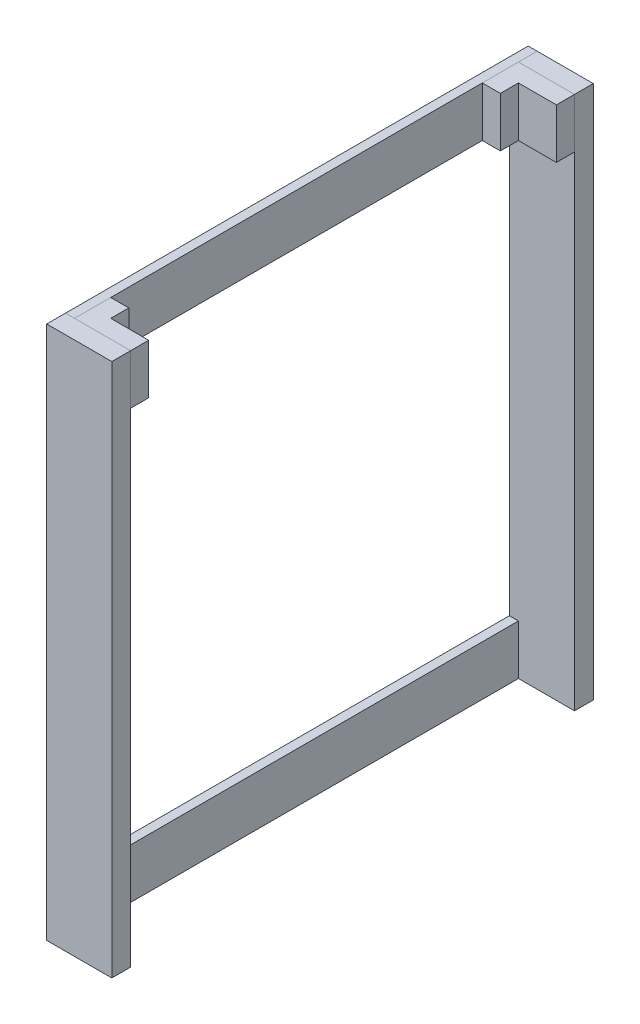
SolidWorks part; units mm, degrees
material "Pine"
ref_plane "Front Plane" through (0, 0, 0) normal (0, 0, 1) x (1, 0, 0)
ref_plane "Top Plane" through (0, 0, 0) normal (0, 1, 0) x (1, 0, 0)
ref_plane "Right Plane" through (0, 0, 0) normal (1, 0, 0) x (0, 0, -1)
sketch "Sketch1" plane through (0, 0, 0) normal (0, 1, 0) x (1, 0, 0)
  line L0 (0, -385) -> (0, 385) construction
  line L1 (-700, 350) -> (700, 350)
  line L2 (-700, 350) -> (-700, -350)
  line L3 (-700, -350) -> (700, -350)
  line L4 (700, 350) -> (700, -350)
  line L6 (-770, 0) -> (770, 0) construction
  dimension "D1" = 700
  dimension "D2" = 1400
  dimension "D3" = 700
  dimension "D4" = 350
ref_plane "Plane1" through (0, -900, 0) normal (0, 1, 0) x (-1, 0, 0)
sketch "Sketch3" plane through (0, -900, 0) normal (0, 1, 0) x (-1, 0, 0)
  line L0 (700, -350) -> (700, 350) construction
  line L1 (700, -350) -> (-700, -350) construction
  line L2 (700, 350) -> (-700, 350) construction
  line L3 (700, 333) -> (610, 333)
  line L4 (700, 333) -> (700, 307)
  line L5 (700, -333) -> (610, -333)
  line L6 (700, -333) -> (700, -307)
  line L7 (700, -307) -> (610, -307)
  line L8 (610, -333) -> (610, -307)
  line L9 (700, 307) -> (610, 307)
  line L10 (610, 333) -> (610, 307)
  dimension "D1" = 26
  dimension "D2" = 90
  dimension "D3" = 17
  dimension "D4" = 17
extrude "Boss-Extrude1" add sketch "Sketch3" along normal offset from surface (738.5 mm away) 31.5 from offset 130 up to plane "Top Plane"
sketch "Sketch5" plane through (0, 0, 0) normal (0, 0, 1) x (1, 0, 0)
  line L1 (-700, -31.5) -> (-687.5, -31.5)
  line L2 (-700, -31.5) -> (-700, -100.5)
  line L3 (-700, -100.5) -> (-687.5, -100.5)
  line L4 (-687.5, -31.5) -> (-687.5, -100.5)
  line L5 (-700, -770) -> (-687.5, -770)
  line L6 (-700, -770) -> (-700, -701)
  line L7 (-700, -701) -> (-687.5, -701)
  line L8 (-687.5, -770) -> (-687.5, -701)
  line L10 (-700, -31.5) -> (-700, -770) construction
  line L11 (-700, -770) -> (-610, -770) construction
  dimension "D1" = 12.5
  dimension "D2" = 69
extrude "Boss-Extrude2" add sketch "Sketch5" along normal up to surface and the other way up to surface separate body
sketch "Sketch7" plane through (0, -31.5, 0) normal (0, 1, 0) x (1, 0, 0)
  line L0 (-687.5, -333) -> (-687.5, 333) construction
  line L1 (-610, 307) -> (-687.5, 307)
  line L2 (-610, 307) -> (-610, 282)
  line L3 (-610, 282) -> (-662.5, 282)
  line L4 (-687.5, 307) -> (-687.5, 282)
  line L5 (-687.5, 282) -> (-687.5, 257)
  line L6 (-610, -307) -> (-687.5, -307)
  line L7 (-610, -307) -> (-610, -282)
  line L8 (-610, -282) -> (-662.5, -282)
  line L9 (-687.5, -307) -> (-687.5, -282)
  line L10 (-687.5, 257) -> (-662.5, 257)
  line L11 (-662.5, 257) -> (-662.5, 282)
  line L12 (-687.5, -282) -> (-687.5, -257)
  line L13 (-687.5, -257) -> (-662.5, -257)
  line L14 (-662.5, -257) -> (-662.5, -282)
  dimension "D1" = 25
extrude "Boss-Extrude3" add sketch "Sketch7" against normal up to surface (69 mm away) separate body up to face at (-693.75, -100.5, 0)
sketch "Sketch8" plane through (0, -770, 0) normal (0, -1, 0) x (1, 0, 0)
  line L0 (-687.5, 333) -> (-687.5, -333) construction
  line L1 (-610, 307) -> (-687.5, 307)
  line L2 (-610, 307) -> (-610, 267)
  line L3 (-610, 267) -> (-687.5, 267)
  line L4 (-687.5, 307) -> (-687.5, 267)
  line L6 (-610, -307) -> (-687.5, -307)
  line L7 (-610, -307) -> (-610, -267)
  line L8 (-610, -267) -> (-687.5, -267)
  line L9 (-687.5, -307) -> (-687.5, -267)
  dimension "D1" = 40
extrude "Boss-Extrude4" [suppressed] add sketch "Sketch8" against normal up to surface (69 mm away) separate body
